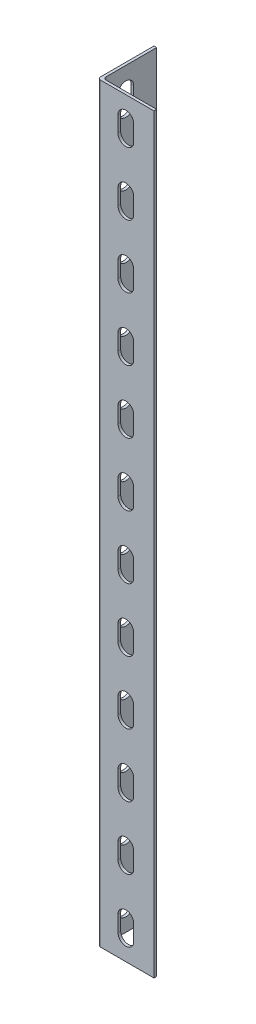
SolidWorks part; units mm, degrees
ref_plane "Front Plane" through (0, 0, 0) normal (0, 0, 1) x (1, 0, 0)
ref_plane "Top Plane" through (0, 0, 0) normal (0, 1, 0) x (1, 0, 0)
ref_plane "Right Plane" through (0, 0, 0) normal (1, 0, 0) x (0, 0, -1)
sketch "Sketch1" plane through (0, 0, 0) normal (0, 1, 0) x (1, 0, 0)
  line L0 (0, 0) -> (0, 25)
  line L1 (0, 0) -> (25, 0)
  dimension "D1" = 25
extrude "Extrude-Thin1" add sketch "Sketch1" along normal blind 350 thin
fillet "Fillet1" radius 1.2 2 edges at (1.2, 175, -1.2) (0, 175, 0)
sketch "Sketch2" plane through (0, 0, 0) normal (0, 0, 1) x (1, 0, 0)
  line L0 (12.5, 9.5) -> (12.5, 16.5) construction
  line L1 (9, 9.5) -> (9, 16.5)
  line L2 (16, 9.5) -> (16, 16.5)
  line L3 (1.2, 0) -> (25, 0) construction
  line L4 (25, 350) -> (25, 0) construction
  arc A0 (9, 9.5) -> (16, 9.5) centre (12.5, 9.5) ccw
  arc A1 (16, 16.5) -> (9, 16.5) centre (12.5, 16.5) ccw
  point P2 (12.5, 13)
  dimension "D1" = 3.5
  dimension "D3" = 9.5
  dimension "D2" = 7
  dimension "D4" = 12.5
extrude "Cut-Extrude1" cut sketch "Sketch2" against normal through all
pattern_linear "LPattern1" count 14 spacing 28 along (0, 1, 0) of "Cut-Extrude1"
pattern_circular "CirPattern1" count 2 every 270 about axis through (1.2, 350, 0) along (0, -1, 0) of "LPattern1", "Cut-Extrude1"
sketch "Sketch5" plane through (0, 350, 0) normal (0, 1, 0) x (1, 0, 0)
  line L0 (0, 14.8) -> (0, 7.8)
  line L1 (1.2, 14.8) -> (1.2, 7.8)
  line L2 (9, 1.2) -> (16, 1.2)
  line L3 (16, 0) -> (9, 0)
  line L4 (0, 25) -> (0, 14.8)
  line L5 (0, 14.8) -> (1.2, 14.8)
  line L6 (1.2, 14.8) -> (1.2, 25)
  line L7 (1.2, 25) -> (0, 25)
  line L8 (0, 25) -> (0, 14.8)
  line L10 (1.2, 14.8) -> (1.2, 25)
  line L11 (1.2, 25) -> (0, 25)
  line L12 (25, 1.2) -> (16, 1.2)
  line L13 (16, 1.2) -> (16, 0)
  line L14 (1.2, 2.4) -> (1.2, 7.8)
  line L15 (1.2, 7.8) -> (0, 7.8)
  line L16 (0, 7.8) -> (0, 1.2)
  line L17 (1.2, 0) -> (9, 0)
  line L18 (9, 0) -> (9, 1.2)
  line L19 (9, 1.2) -> (2.4, 1.2)
  line L20 (1.2, 2.4) -> (1.2, 7.8)
  line L22 (0, 7.8) -> (0, 1.2)
  line L23 (1.2, 0) -> (9, 0)
  line L25 (10.4404, 1.2) -> (2.4, 1.2)
  line L26 (16, 0) -> (25, 0)
  line L27 (25, 0) -> (25, 1.2)
  line L28 (25, 1.2) -> (16, 1.2)
  line L30 (16, 0) -> (25, 0)
  line L31 (25, 0) -> (25, 1.2)
  arc A2 (0, 1.2) -> (1.2, 0) centre (1.2, 1.2) ccw
  arc A3 (1.2, 2.4) -> (2.4, 1.2) centre (2.4, 2.4) ccw
  arc A4 (0, 1.2) -> (1.2, 0) centre (1.2, 1.2) ccw
  arc A5 (1.2, 2.4) -> (2.4, 1.2) centre (2.4, 2.4) ccw
  line M17 (0, 25) -> (0, 14.8)
  line M18 (0, 14.8) -> (1.2, 14.8)
  line M19 (1.2, 14.8) -> (1.2, 25)
  line M20 (1.2, 25) -> (0, 25)
  dimension "D1" = 0
  dimension "D2" = 0
  dimension "D3" = 0
extrude "Cut-Extrude3" cut sketch "Sketch5" against normal blind 16 contours A5 L20 L1 L0 L22 A4 L23 L3 L30 L31 L28 L2 L25 M18 | M20 M17 M18 M19
